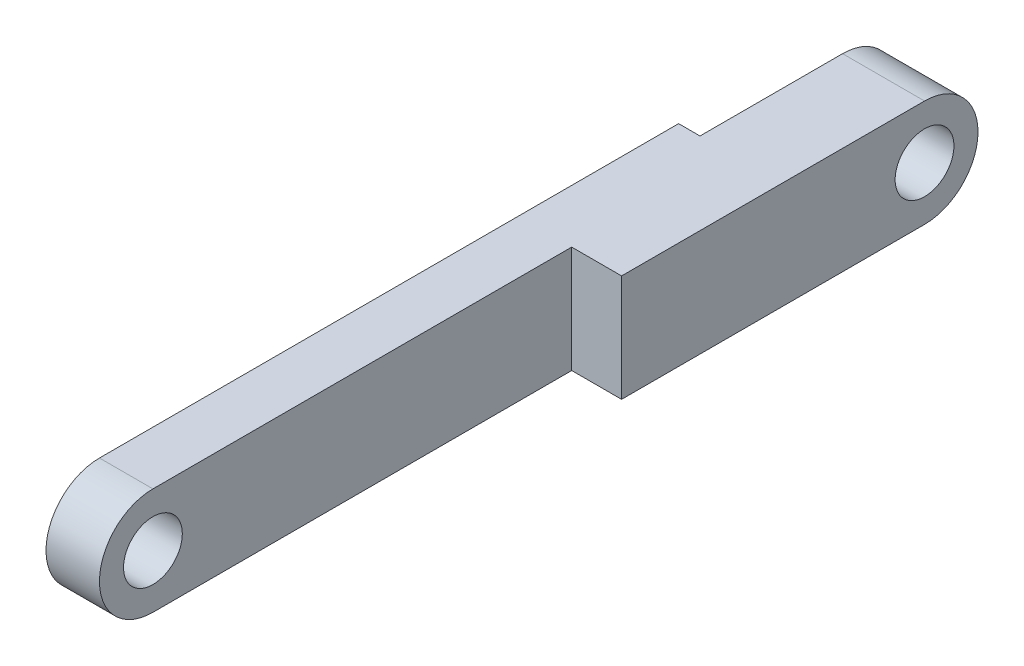
SolidWorks part; units mm, degrees
material "Plain Carbon Steel"
ref_plane "Front Plane" through (0, 0, 0) normal (0, 0, 1) x (1, 0, 0)
ref_plane "Top Plane" through (0, 0, 0) normal (0, 1, 0) x (1, 0, 0)
ref_plane "Right Plane" through (0, 0, 0) normal (1, 0, 0) x (0, 0, -1)
sketch "Sketch1" plane through (0, 0, 0) normal (1, 0, 0) x (0, 0, -1)
  line L24 (0, 3) -> (40.5, 3)
  line L25 (0, -3) -> (40.5, -3)
  arc A6 (0, 3) -> (0, -3) centre (0, 0) ccw
  arc A8 (40.5, 3) -> (40.5, -3) centre (40.5, 0) cw
  circle A10 centre (0, 0) radius 1.65
  circle A11 centre (40.5, 0) radius 1.65
  dimension "D1" = 6
  dimension "D2" = 40.5
  dimension "D3" = 3.3
extrude "Boss-Extrude1" add sketch "Sketch1" along normal blind 3
sketch "Sketch3" plane through (0, 0, 0) normal (-1, 0, 0) x (0, 0, 1)
  line L0 (-43.5, 3) -> (-32.5, 3)
  line L1 (-40.5, 3) -> (0, 3) construction
  line L2 (-32.5, 3) -> (-32.5, -3)
  line L3 (0, -3) -> (-40.5, -3) construction
  line L4 (-32.5, -3) -> (-43.5, -3)
  line L5 (-43.5, -3) -> (-43.5, 3)
  arc A1 (-40.5, 3) -> (-40.5, -3) centre (-40.5, 0) ccw construction
  dimension "D1" = 11
extrude "Cut-Extrude2" cut sketch "Sketch3" against normal blind 1.2
sketch "Sketch4" plane through (3, 0, 0) normal (1, 0, 0) x (0, 0, -1)
  line L0 (23.5, 3) -> (23.5, -3)
  line L5 (0, -3) -> (40.5, -3)
  line L6 (40.5, 3) -> (0, 3)
  line L7 (0, -3) -> (23.5, -3)
  line L8 (23.5, 3) -> (0, 3)
  arc A1 (40.5, -3) -> (40.5, 3) centre (40.5, 0) ccw construction
  arc A2 (0, 3) -> (0, -3) centre (0, 0) ccw
  arc A3 (40.5, -3) -> (40.5, 3) centre (40.5, 0) ccw
  arc A4 (0, 3) -> (0, -3) centre (0, 0) ccw
  circle M1 centre (40.5, 0) radius 1.65
  line M3 (0, -3) -> (40.5, -3)
  arc M4 (40.5, -3) -> (40.5, 3) centre (40.5, 0) ccw
  line M5 (40.5, 3) -> (0, 3)
  dimension "D2" = 17
  dimension "D1" = 0
extrude "Boss-Extrude2" add sketch "Sketch4" along normal blind 2.8 contours L0 M5 M3 M4 M1
